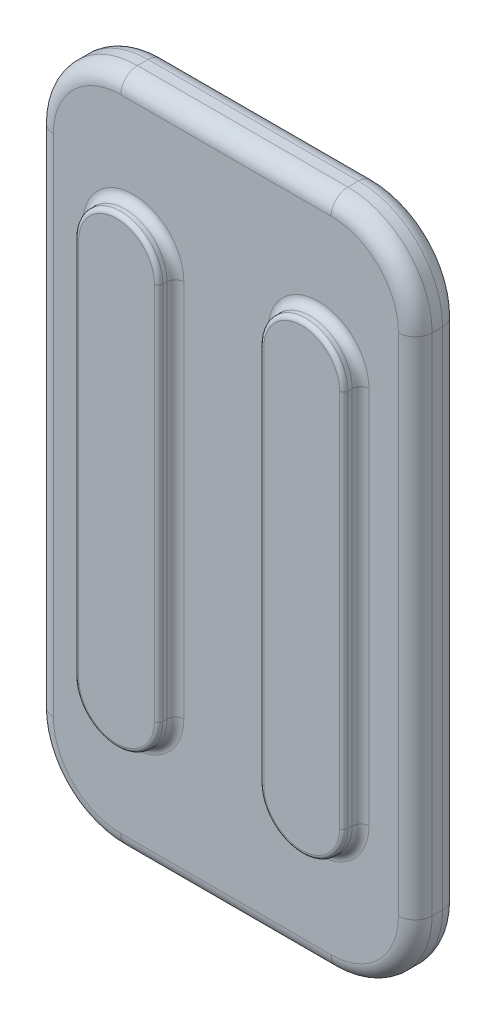
SolidWorks part; units mm, degrees
ref_plane "前视基准面" through (0, 0, 0) normal (0, 0, 1) x (1, 0, 0)
ref_plane "上视基准面" through (0, 0, 0) normal (0, 1, 0) x (1, 0, 0)
ref_plane "右视基准面" through (0, 0, 0) normal (1, 0, 0) x (0, 0, -1)
sketch "草图1" plane through (0, 0, 0) normal (0, 0, 1) x (1, 0, 0)
  line L1 (-225, 400) -> (225, 400)
  line L2 (-225, 400) -> (-225, -400)
  line L3 (-225, -400) -> (225, -400)
  line L4 (225, 400) -> (225, -400)
  line L5 (-225, 400) -> (225, -400) construction
  line L6 (-225, -400) -> (225, 400) construction
  point P0 (0, 0)
  dimension "D1" = 450
  dimension "D2" = 800
extrude "凸台-拉伸1" add sketch "草图1" along normal blind 52.4849
sketch "草图2" plane through (0, 0, 52.4849) normal (0, 0, 1) x (1, 0, 0)
  line L0 (0, 400) -> (0, -400) construction
  line L1 (225, 400) -> (-225, 400) construction
  line L2 (-225, -400) -> (225, -400) construction
  line L3 (-110, 225) -> (-110, -225) construction
  line L4 (-60, 225) -> (-60, -225)
  line L5 (-160, 225) -> (-160, -225)
  line L6 (110, 225) -> (110, -225) construction
  line L7 (60, 225) -> (60, -225)
  line L8 (160, 225) -> (160, -225)
  arc A0 (-60, 225) -> (-160, 225) centre (-110, 225) ccw
  arc A1 (-160, -225) -> (-60, -225) centre (-110, -225) ccw
  arc A2 (60, 225) -> (160, 225) centre (110, 225) cw
  arc A3 (160, -225) -> (60, -225) centre (110, -225) cw
  point P8 (-110, 0)
  point P16 (110, 0)
  dimension "D2" = 50
  dimension "D1" = 450
  dimension "D3" = 110
extrude "凸台-拉伸2" add sketch "草图2" along normal blind 20
fillet "圆角1" radius 100 4 edges at (225, 400, 26.2425) (-225, 400, 26.2425) (225, -400, 26.2425) (-225, -400, 26.2425)
fillet "圆角2" radius 10 8 edges at (110, 275, 52.4849) (160, 0, 52.4849) (110, -275, 52.4849) (-110, 275, 52.4849) (-60, 0, 52.4849) (-110, -275, 52.4849) (60, 0, 52.4849) (-160, 0, 52.4849)
fillet "圆角3" radius 5 8 edges at (-60, 0, 72.4849) (-110, -275, 72.4849) (-160, 0, 72.4849) (-110, 275, 72.4849) (160, 0, 72.4849) (110, -275, 72.4849) (60, 0, 72.4849) (110, 275, 72.4849)
fillet "圆角4" radius 20 16 edges at (-195.7107, 370.7107, 0) (0, 400, 0) (195.7107, 370.7107, 0) (225, 0, 0) (195.7107, -370.7107, 0) (0, -400, 0) (-195.7107, -370.7107, 0) (-195.7107, 370.7107, 52.4849) (0, 400, 52.4849) (195.7107, 370.7107, 52.4849) (225, 0, 52.4849) (195.7107, -370.7107, 52.4849) (0, -400, 52.4849) (-195.7107, -370.7107, 52.4849) (-225, 0, 0) (-225, 0, 52.4849)
sketch "草图3" plane through (0, 400, 0) normal (0, 1, 0) x (1, 0, 0)
  line L0 (0, 0) -> (0, 122.9159) construction
  line L1 (-159.75, 0) -> (-110.25, 0)
  line L2 (-125, 0) -> (-205, 0) construction
  line L3 (125, 0) -> (-125, 0) construction
  line L4 (-110.25, 0) -> (-110.25, 7.38)
  line L5 (-110.25, 7.38) -> (-122.225, 19.39)
  line L6 (-122.225, 19.39) -> (-147.775, 19.39)
  line L7 (-135, 0) -> (-135, 19.39) construction
  line L8 (-159.75, 7.38) -> (-147.775, 19.39)
  line L9 (-159.75, 0) -> (-159.75, 7.38)
  line L10 (135, 0) -> (135, 19.39) construction
  line L11 (159.75, 0) -> (159.75, 7.38)
  line L12 (159.75, 7.38) -> (147.775, 19.39)
  line L13 (122.225, 19.39) -> (147.775, 19.39)
  line L14 (110.25, 7.38) -> (122.225, 19.39)
  line L15 (110.25, 0) -> (110.25, 7.38)
  line L16 (159.75, 0) -> (110.25, 0)
  dimension "D1" = 49.5
  dimension "D2" = 25.55
  dimension "D3" = 7.38
  dimension "D4" = 19.39
  dimension "D5" = 220.5
extrude "凸台-拉伸3" add sketch "草图3" against normal blind 670 from offset 100 offset against normal yes
